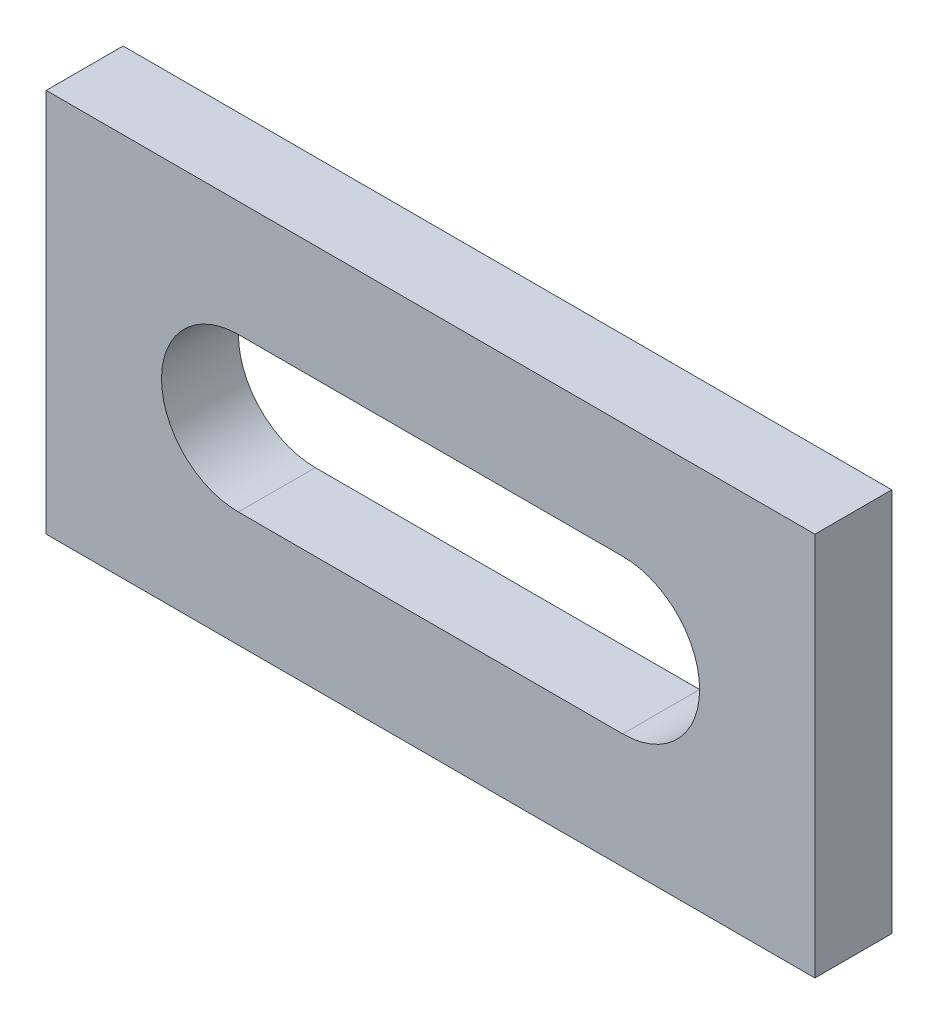
SolidWorks part; units mm, degrees
ref_plane "Front Plane" through (0, 0, 0) normal (0, 0, 1) x (1, 0, 0)
ref_plane "Top Plane" through (0, 0, 0) normal (0, 1, 0) x (1, 0, 0)
ref_plane "Right Plane" through (0, 0, 0) normal (1, 0, 0) x (0, 0, -1)
sketch "Sketch2" plane through (0, 0, 0) normal (0, 0, 1) x (1, 0, 0)
  line L1 (-50, -25) -> (50, -25)
  line L2 (-50, -25) -> (-50, 25)
  line L3 (-50, 25) -> (50, 25)
  line L4 (50, -25) -> (50, 25)
  line L5 (-50, -25) -> (50, 25) construction
  line L6 (-50, 25) -> (50, -25) construction
  point P0 (0, 0)
  dimension "D1" = 50
  dimension "D2" = 100
extrude "Box" add sketch "Sketch2" along normal mid plane 10
sketch "Sketch3" plane through (0, 0, 0) normal (0, 0, 1) x (1, 0, 0)
  line L0 (-25, 0) -> (25, 0) construction
  line L1 (-25, 10) -> (25, 10)
  line L2 (-25, -10) -> (25, -10)
  arc A0 (-25, 10) -> (-25, -10) centre (-25, 0) ccw
  arc A1 (25, -10) -> (25, 10) centre (25, 0) ccw
  point P2 (0, 0)
  dimension "D1" = 50
  dimension "D2" = 20
extrude "Hole" cut sketch "Sketch3" against normal through all both and the other way through all
